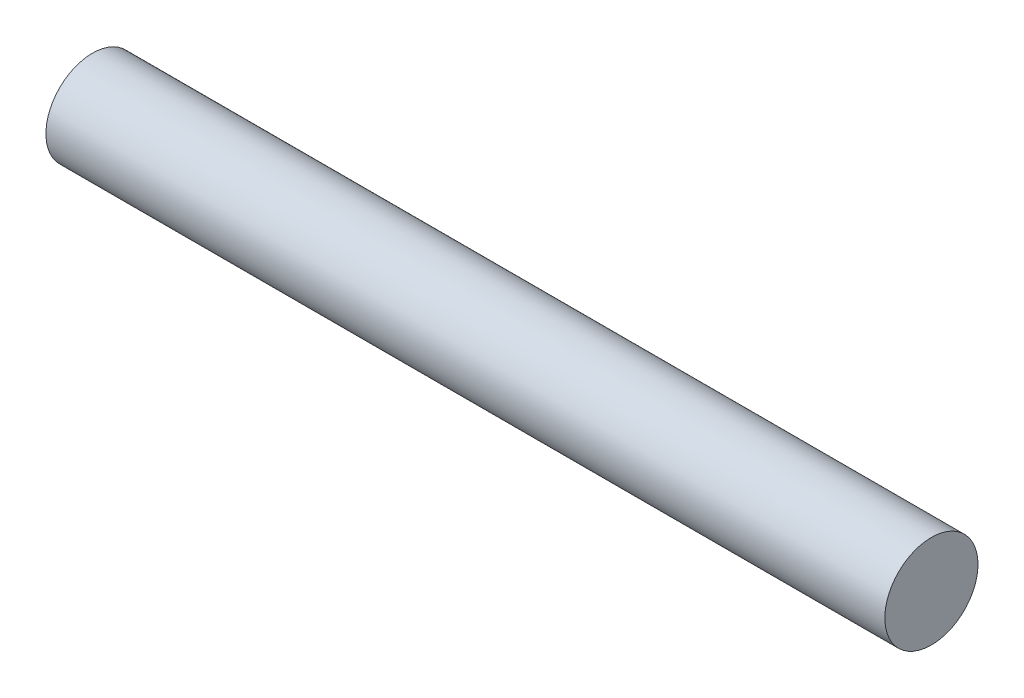
SolidWorks part; units mm, degrees
material "Alloy Steel"
ref_plane "Front" through (0, 0, 0) normal (0, 0, 1) x (1, 0, 0)
ref_plane "Top" through (0, 0, 0) normal (0, 1, 0) x (1, 0, 0)
ref_plane "Right" through (0, 0, 0) normal (1, 0, 0) x (0, 0, -1)
sketch "Sketch1" plane through (0, 0, 0) normal (1, 0, 0) x (0, 0, -1)
  circle A0 centre (0, 0) radius 10
  dimension "D1" = 20
extrude "Boss-Extrude1" add sketch "Sketch1" along normal blind 180
